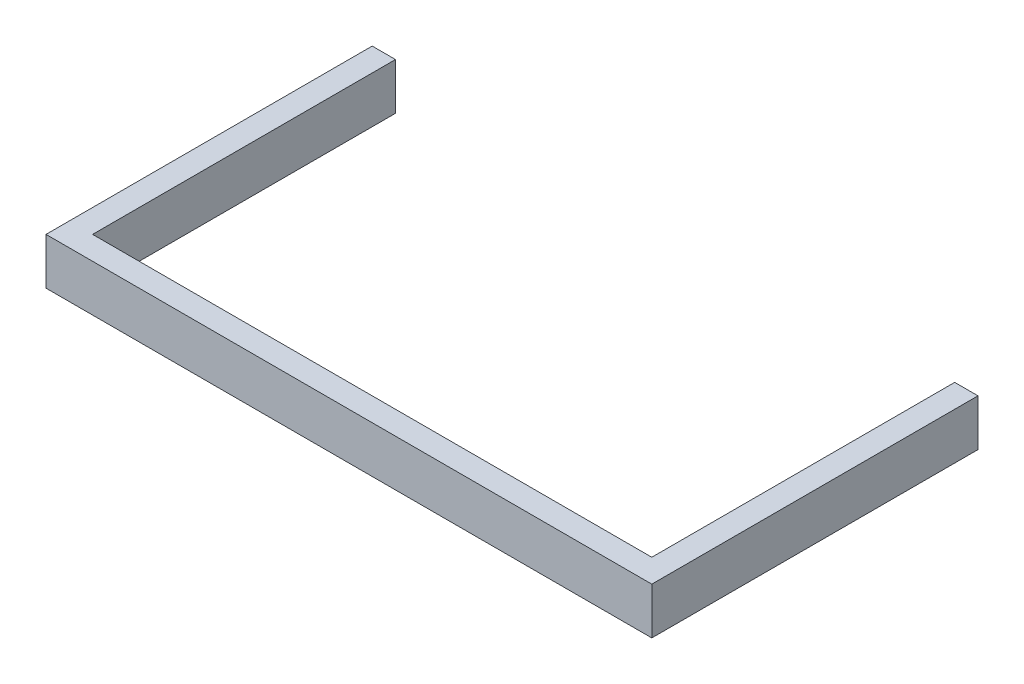
SolidWorks part; units mm, degrees
ref_plane "Front Plane" through (0, 0, 0) normal (0, 0, 1) x (1, 0, 0)
ref_plane "Top Plane" through (0, 0, 0) normal (0, 1, 0) x (1, 0, 0)
ref_plane "Right Plane" through (0, 0, 0) normal (1, 0, 0) x (0, 0, -1)
sketch "Sketch1" plane through (0, 0, 0) normal (0, 1, 0) x (1, 0, 0)
  line L1 (0, 0) -> (660.4, 0)
  line L2 (0, 0) -> (0, 25.4)
  line L3 (25.4, 25.4) -> (166.006, 25.4)
  line L4 (660.4, 0) -> (660.4, 25.4)
  line L5 (0, 0) -> (25.4, 0)
  line L6 (0, 0) -> (0, 355.6)
  line L7 (0, 355.6) -> (25.4, 355.6)
  line L8 (25.4, 25.4) -> (25.4, 339.6476)
  line L9 (660.4, 0) -> (635, 0)
  line L10 (660.4, 0) -> (660.4, 355.6)
  line L11 (660.4, 355.6) -> (635, 355.6)
  line L12 (635, 25.4) -> (635, 339.6476)
  line L14 (46.7473, 355.6) -> (25.4, 355.6)
  line L15 (196.9175, 25.4) -> (166.006, 25.4)
  line L16 (613.6527, 355.6) -> (635, 355.6)
  line L19 (494.394, 25.4) -> (635, 25.4)
  line L20 (196.9175, 25.4) -> (463.4825, 25.4)
  line L21 (25.4, 339.6476) -> (25.4, 355.6)
  line L22 (635, 339.6476) -> (635, 355.6)
  line L23 (463.4825, 25.4) -> (494.394, 25.4)
  point P8 (12.7, 355.6)
  dimension "D1" = 660.4
  dimension "D2" = 330.2
  dimension "D3" = 25.4
  dimension "D4" = 330.2
  dimension "D5" = 25.4
  dimension "D6" = 314.2476
  dimension "D7" = 25.4
  dimension "D9" = 330.2
extrude "Boss-Extrude1" add sketch "Sketch1" along normal blind 50.8 contours L23 L20 L15 L3 L8 L21 L7 L6 L2 L1 L4 L10 L11 L22 L12 L19
